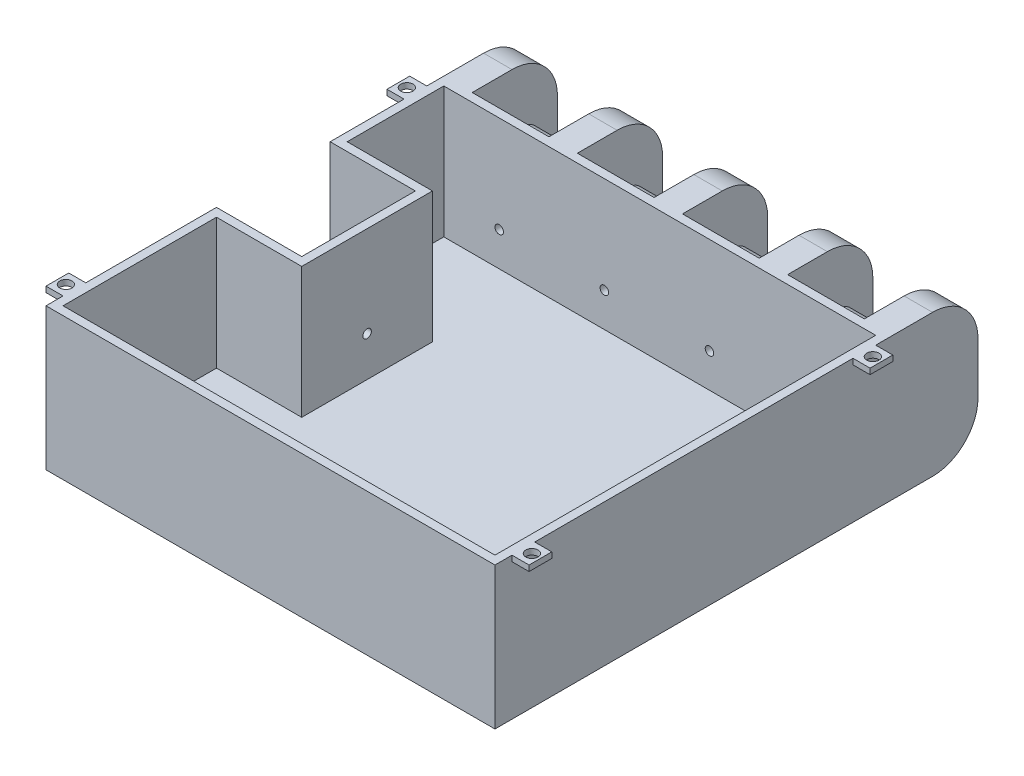
SolidWorks part; units mm, degrees
ref_plane "Front Plane" through (0, 0, 0) normal (0, 0, 1) x (1, 0, 0)
ref_plane "Top Plane" through (0, 0, 0) normal (0, 1, 0) x (1, 0, 0)
ref_plane "Right Plane" through (0, 0, 0) normal (1, 0, 0) x (0, 0, -1)
sketch "Sketch2" plane through (0, 0, 0) normal (0, 1, 0) x (1, 0, 0)
  line L0 (0, 0) -> (79, 0)
  line L1 (79, 0) -> (79, 85)
  line L2 (79, 85) -> (74, 85)
  line L3 (74, 85) -> (74, 70)
  line L4 (74, 70) -> (60.5, 70)
  line L5 (60.5, 70) -> (60.5, 85)
  line L6 (60.5, 85) -> (55.5, 85)
  line L7 (55.5, 85) -> (55.5, 70)
  line L8 (55.5, 70) -> (42, 70)
  line L9 (42, 70) -> (42, 85)
  line L10 (42, 85) -> (37, 85)
  line L11 (37, 85) -> (37, 70)
  line L12 (37, 70) -> (23.5, 70)
  line L13 (23.5, 70) -> (23.5, 85)
  line L14 (23.5, 85) -> (18.5, 85)
  line L15 (18.5, 85) -> (18.5, 70)
  line L16 (18.5, 70) -> (5, 70)
  line L17 (5, 70) -> (5, 85)
  line L18 (5, 85) -> (0, 85)
  line L19 (0, 85) -> (0, 50)
  line L20 (0, 50) -> (15, 50)
  line L21 (15, 50) -> (15, 30)
  line L22 (15, 30) -> (0, 30)
  line L23 (0, 30) -> (0, 0)
  dimension "D1" = 5
  dimension "D2" = 5
  dimension "D3" = 5
  dimension "D4" = 79
  dimension "D5" = 5
  dimension "D6" = 5
  dimension "D7" = 13.5
  dimension "D8" = 13.5
  dimension "D9" = 13.5
  dimension "D10" = 85
  dimension "D11" = 85
  dimension "D12" = 15
  dimension "D13" = 15
  dimension "D14" = 15
  dimension "D15" = 15
  dimension "D16" = 15
  dimension "D17" = 15
  dimension "D18" = 15
  dimension "D19" = 20
  dimension "D20" = 20
  dimension "D21" = 15
extrude "Boss-Extrude1" add sketch "Sketch2" along normal blind 25
sketch "Sketch3" plane through (74, 0, 0) normal (-1, 0, 0) x (0, 0, 1)
  line L0 (-85, 25) -> (-85, 0) construction
  line L1 (-85, 0) -> (-70, 0) construction
  circle A0 centre (-79, 12.5) radius 2.8
  dimension "D3" = 5.6
  dimension "D1" = 6
  dimension "D2" = 12.5
extrude "Boss-Extrude2" add sketch "Sketch3" along normal blind 69
sketch "Sketch4" plane through (0, 25, 0) normal (0, 1, 0) x (1, 0, 0)
  line L0 (0, 50) -> (15, 50)
  line L1 (15, 50) -> (15, 30)
  line L2 (15, 30) -> (0, 30)
  line L3 (0, 30) -> (0, 0)
  line L4 (0, 0) -> (79, 0)
  line L5 (79, 0) -> (79, 70)
  line L6 (79, 0) -> (79, 85) construction
  line L7 (79, 70) -> (0, 70)
  line L8 (0, 85) -> (0, 50) construction
  line L9 (0, 70) -> (0, 50)
  line L10 (1.5, 68.5) -> (1.5, 51.5)
  line L11 (1.5, 51.5) -> (16.5, 51.5)
  line L12 (16.5, 51.5) -> (16.5, 28.5)
  line L13 (16.5, 28.5) -> (1.5, 28.5)
  line L14 (1.5, 28.5) -> (1.5, 1.5)
  line L15 (1.5, 1.5) -> (77.5, 1.5)
  line L16 (77.5, 1.5) -> (77.5, 68.5)
  line L17 (77.5, 68.5) -> (1.5, 68.5)
  point P26 (0, 0)
  point P27 (0, 0)
  dimension "D1" = 70
  dimension "D2" = 1.5
extrude "Cut-Extrude2" cut sketch "Sketch4" against normal blind 23 contours L10 L11 L12 L13 L14 L15 L16 L17
sketch "Sketch9" plane through (0, 0, -50) normal (0, 0, 1) x (1, 0, 0)
  line L0 (0, 25) -> (15, 25) construction
  line L1 (0, 25) -> (0, 0) construction
  circle A0 centre (7.5, 12.5) radius 2.311
  dimension "D1" = 12.5
  dimension "D2" = 7.5
extrude "Boss-Extrude3" add sketch "Sketch9" along normal blind 20
fillet "Fillet1" radius 8 10 edges at (2.5, 0, -85) (21, 0, -85) (39.5, 0, -85) (58, 0, -85) (76.5, 0, -85) (76.5, 25, -85) (58, 25, -85) (39.5, 25, -85) (21, 25, -85) (2.5, 25, -85)
sketch "Sketch10" plane through (0, 0, -68.5) normal (0, 0, 1) x (1, 0, 0)
  line L0 (77.5, 25) -> (1.5, 25) construction
  line L1 (1.5, 2) -> (1.5, 25) construction
  circle A0 centre (11.25, 8) radius 0.75
  dimension "D1" = 1.5
  dimension "D2" = 17
  dimension "D3" = 9.75
extrude "Cut-Extrude4" cut sketch "Sketch10" against normal blind 2 contours A0
pattern_linear "LPattern2" count 2 spacing 2 along (0, 0, 1) count 4 spacing 18.5 along (1, 0, 0) of "Cut-Extrude4"
sketch "Sketch11" plane through (16.5, 0, 0) normal (1, 0, 0) x (0, 0, -1)
  line L1 (28.5, 2) -> (28.5, 25) construction
  line L2 (51.5, 25) -> (28.5, 25) construction
  circle A0 centre (40, 9) radius 0.75
  dimension "D3" = 1.5
  dimension "D1" = 11.5
  dimension "D2" = 16
extrude "Cut-Extrude5" cut sketch "Sketch11" against normal blind 2
sketch "Sketch13" plane through (79, 0, 0) normal (1, 0, 0) x (0, 0, -1)
  line L0 (0, 25) -> (77, 25) construction
  line L1 (3, 25) -> (7, 25)
  line L2 (3, 25) -> (3, 24)
  line L3 (3, 24) -> (7, 24)
  line L4 (7, 25) -> (7, 24)
  line L5 (0, 25) -> (0, 0) construction
  dimension "D1" = 1
  dimension "D2" = 4
  dimension "D3" = 3
extrude "Boss-Extrude4" add sketch "Sketch13" along normal blind 3
sketch "Sketch14" plane through (0, 24, 0) normal (0, -1, 0) x (-1, 0, 0)
  line L0 (-82, 3) -> (-82, 7) construction
  line L1 (-82, 7) -> (-79, 7) construction
  circle A0 centre (-80.5, 5) radius 1.0783
  dimension "D1" = 1.5
  dimension "D2" = 2
extrude "Cut-Extrude6" cut sketch "Sketch14" against normal through all contours A0
pattern_linear "LPattern3" count 2 spacing 60 along (0, 0, -1) count 2 spacing 82 along (-1, 0, 0) of "Boss-Extrude4"
pattern_linear "LPattern4" count 2 spacing 60 along (0, 0, -1) count 2 spacing 82 along (-1, 0, 0) of "Cut-Extrude6"
